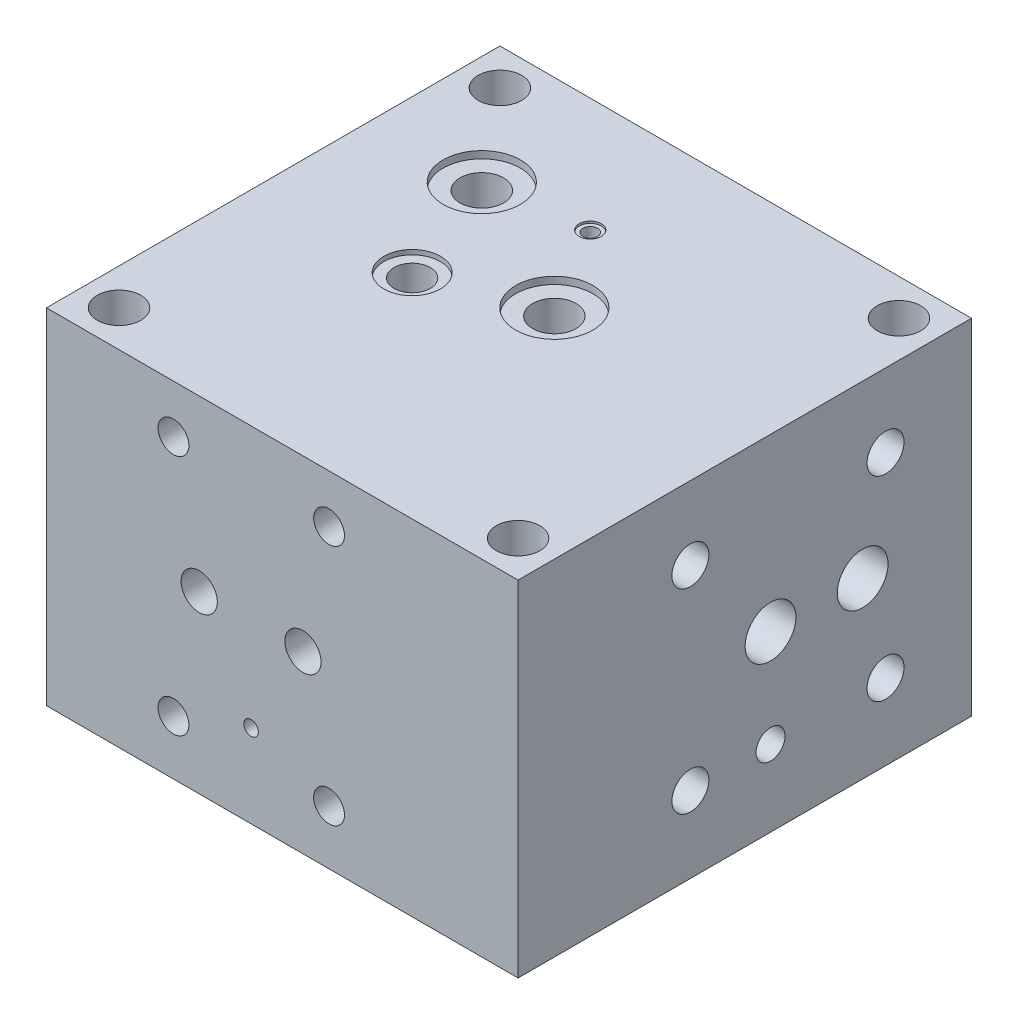
SolidWorks part; units mm, degrees
ref_plane "前视基准面" through (0, 0, 0) normal (0, 0, 1) x (1, 0, 0)
ref_plane "上视基准面" through (0, 0, 0) normal (0, 1, 0) x (1, 0, 0)
ref_plane "右视基准面" through (0, 0, 0) normal (1, 0, 0) x (0, 0, -1)
sketch "草图1" plane through (0, 0, 0) normal (0, 1, 0) x (1, 0, 0)
  line L1 (65, -62.5) -> (-65, -62.5)
  line L2 (65, -62.5) -> (65, 62.5)
  line L3 (65, 62.5) -> (-65, 62.5)
  line L4 (-65, -62.5) -> (-65, 62.5)
  line L5 (65, -62.5) -> (-65, 62.5) construction
  line L6 (65, 62.5) -> (-65, -62.5) construction
  point P0 (0, 0)
  dimension "D1" = 130
  dimension "D2" = 125
extrude "凸台-拉伸2" add sketch "草图1" along normal blind 95
sketch "草图2" plane through (0, 95, 0) normal (0, 1, 0) x (1, 0, 0)
  line L0 (-65, 62.5) -> (-65, -62.5) construction
  line L1 (65, 62.5) -> (-65, 62.5) construction
  line L2 (65, -62.5) -> (65, 62.5) construction
  line L3 (-65, -62.5) -> (65, -62.5) construction
  circle A0 centre (-55, 52.5) radius 6
  circle A1 centre (55, 52.5) radius 6
  circle A2 centre (-55, -52.5) radius 6
  dimension "D3" = 12
  dimension "D4" = 10
  dimension "D6" = 10
  dimension "D1" = 10
  dimension "D2" = 10
  dimension "D5" = 10
  dimension "D7" = 10
extrude "切除-拉伸1" cut sketch "草图2" against normal through all
sketch "草图3" plane through (0, 95, 0) normal (0, 1, 0) x (1, 0, 0)
  line L0 (65, -62.5) -> (65, 62.5) construction
  line L1 (-65, -62.5) -> (65, -62.5) construction
  circle A0 centre (55, -52.5) radius 6
  dimension "D1" = 10
  dimension "D2" = 10
extrude "切除-拉伸2" cut sketch "草图3" against normal blind 95
sketch "草图4" plane through (0, 95, 0) normal (0, 1, 0) x (1, 0, 0)
  line L0 (65, 62.5) -> (-65, 62.5) construction
  line L1 (-65, 62.5) -> (-65, -62.5) construction
  circle A0 centre (-35, 27.5) radius 10.65
  dimension "D1" = 21.3
  dimension "D2" = 35
  dimension "D3" = 30
extrude "切除-拉伸3" cut sketch "草图4" against normal blind 1.97
sketch "草图5" plane through (0, 93.03, 0) normal (0, 1, 0) x (1, 0, 0)
  circle A0 centre (-35, 27.5) radius 6
  dimension "D1" = 12
extrude "切除-拉伸5" cut sketch "草图5" against normal through all
sketch "草图6" plane through (0, 95, 0) normal (0, 1, 0) x (1, 0, 0)
  line L1 (-65, 62.5) -> (-65, -62.5) construction
  line L2 (-65, -62.5) -> (65, -62.5) construction
  circle A0 centre (5, 7.5) radius 10.65
  dimension "D1" = 21.3
  dimension "D2" = 70
  dimension "D3" = 70
extrude "切除-拉伸6" cut sketch "草图6" against normal blind 1.97
sketch "草图7" plane through (0, 93.03, 0) normal (0, 1, 0) x (1, 0, 0)
  circle A0 centre (5, 7.5) radius 6
extrude "切除-拉伸7" cut sketch "草图7" against normal through all
sketch "草图8" plane through (0, 95, 0) normal (0, 1, 0) x (1, 0, 0)
  line L0 (-65, -62.5) -> (65, -62.5) construction
  line L1 (-65, 62.5) -> (-65, -62.5) construction
  circle A0 centre (-23, -3.7) radius 7.8
  dimension "D1" = 15.6
  dimension "D2" = 58.8
  dimension "D3" = 42
extrude "切除-拉伸8" cut sketch "草图8" against normal blind 1.28
sketch "草图9" plane through (0, 93.72, 0) normal (0, 1, 0) x (1, 0, 0)
  circle A0 centre (-23, -3.7) radius 5
hole_wizard "大小mm 暗销孔1" positions "3D草图1" profile "草图10" hole size "Ø10.0" standard "GB"
sketch3d "3D草图1"
  point P0 (-23, 93.72, 3.7)
sketch "草图10" plane through (-23, 93.72, 3.7) normal (1, 0, 0) x (0, 0, 1)
  line L0 (0, 0) -> (0, 52.7343)
  line L1 (0, 52.7343) -> (5, 49.73)
  line L2 (5, 49.73) -> (5, 0)
  line L5 (5, 0) -> (0, 0)
  line L10 (0, 52.7343) -> (-5, 49.73) construction
  line L11 (0, -6.35) -> (0, 107.95) construction
  dimension "孔直径" = 10
  dimension "孔深度" = 49.73
  dimension "导头角度" = 118
hole_wizard "M10 螺纹孔2" positions "3D草图3" profile "草图12" tap size "M10" standard "GB"
sketch3d "3D草图3"
  line L0 (-65, 95, 62.5) -> (-65, 0, 62.5) construction
  line L1 (-65, 95, -62.5) -> (-65, 95, 62.5) construction
  point P0 (-65, 81.7, 39.4)
  dimension "D1" = 23.1
  dimension "D2" = 13.3
sketch "草图12" plane through (-65, 81.7, 39.4) normal (0, 1, 0) x (0, 0, 1)
  line L0 (0, 0) -> (0, 16.5537)
  line L1 (0, 16.5537) -> (4.25, 14)
  line L2 (4.25, 14) -> (4.25, 0)
  line L5 (4.25, 0) -> (0, 0)
  line L10 (0, 16.5537) -> (-4.25, 14) construction
  line L11 (0, -6.35) -> (0, 107.95) construction
  dimension "螺纹孔钻头直径" = 8.5
  dimension "螺纹孔钻头深度" = 14
  dimension "导头角度" = 118
cosmetic thread "孔螺蚊线2" parameters "D1"=10, "D2"=10
hole_wizard "M10 螺纹孔3" positions "3D草图4" profile "草图13" tap size "M10" standard "GB"
sketch3d "3D草图4"
  line L0 (-65, 95, -62.5) -> (-65, 95, 62.5) construction
  line L1 (-65, 95, -62.5) -> (-65, 0, -62.5) construction
  point P0 (-65, 81.7, -3.5)
  dimension "D1" = 13.3
  dimension "D2" = 59
sketch "草图13" plane through (-65, 81.7, -3.5) normal (0, 1, 0) x (0, 0, 1)
  line L0 (0, 0) -> (0, 16.5537)
  line L1 (0, 16.5537) -> (4.25, 14)
  line L2 (4.25, 14) -> (4.25, 0)
  line L5 (4.25, 0) -> (0, 0)
  line L10 (0, 16.5537) -> (-4.25, 14) construction
  line L11 (0, -6.35) -> (0, 107.95) construction
  dimension "螺纹孔钻头直径" = 8.5
  dimension "螺纹孔钻头深度" = 14
  dimension "导头角度" = 118
cosmetic thread "孔螺蚊线3" parameters "D1"=10, "D2"=10
hole_wizard "M10 螺纹孔4" positions "3D草图5" profile "草图14" tap size "M10" standard "GB"
sketch3d "3D草图5"
  line L0 (-65, 95, 62.5) -> (-65, 0, 62.5) construction
  line L1 (-65, 0, -62.5) -> (-65, 0, 62.5) construction
  point P0 (-65, 15, 39.4)
  dimension "D1" = 23.1
  dimension "D2" = 15
sketch "草图14" plane through (-65, 15, 39.4) normal (0, 1, 0) x (0, 0, 1)
  line L0 (0, 0) -> (0, 16.5537)
  line L1 (0, 16.5537) -> (4.25, 14)
  line L2 (4.25, 14) -> (4.25, 0)
  line L5 (4.25, 0) -> (0, 0)
  line L10 (0, 16.5537) -> (-4.25, 14) construction
  line L11 (0, -6.35) -> (0, 107.95) construction
  dimension "螺纹孔钻头直径" = 8.5
  dimension "螺纹孔钻头深度" = 14
  dimension "导头角度" = 118
cosmetic thread "孔螺蚊线4" parameters "D1"=10, "D2"=10
hole_wizard "M10 螺纹孔5" positions "3D草图6" profile "草图15" tap size "M10" standard "GB"
sketch3d "3D草图6"
  line L0 (-65, 0, -62.5) -> (-65, 0, 62.5) construction
  line L1 (-65, 95, -62.5) -> (-65, 0, -62.5) construction
  point P0 (-65, 15, -3.5)
  dimension "D1" = 15
  dimension "D2" = 59
sketch "草图15" plane through (-65, 15, -3.5) normal (0, 1, 0) x (0, 0, 1)
  line L0 (0, 0) -> (0, 16.5537)
  line L1 (0, 16.5537) -> (4.25, 14)
  line L2 (4.25, 14) -> (4.25, 0)
  line L5 (4.25, 0) -> (0, 0)
  line L10 (0, 16.5537) -> (-4.25, 14) construction
  line L11 (0, -6.35) -> (0, 107.95) construction
  dimension "螺纹孔钻头直径" = 8.5
  dimension "螺纹孔钻头深度" = 14
  dimension "导头角度" = 118
cosmetic thread "孔螺蚊线5" parameters "D1"=10, "D2"=10
hole_wizard "大小mm 暗销孔2" positions "3D草图7" profile "草图16" hole size "Ø8.0" standard "GB"
sketch3d "3D草图7"
  line L0 (-65, 95, -62.5) -> (-65, 95, 62.5) construction
  line L1 (-65, 95, -62.5) -> (-65, 0, -62.5) construction
  point P0 (-65, 81.7, 12.5)
  dimension "D1" = 13.3
  dimension "D2" = 75
sketch "草图16" plane through (-65, 81.7, 12.5) normal (0, 1, 0) x (0, 0, 1)
  line L0 (0, 0) -> (0, 12.4034)
  line L1 (0, 12.4034) -> (4, 10)
  line L2 (4, 10) -> (4, 0)
  line L5 (4, 0) -> (0, 0)
  line L10 (0, 12.4034) -> (-4, 10) construction
  line L11 (0, -6.35) -> (0, 107.95) construction
  dimension "孔直径" = 8
  dimension "孔深度" = 10
  dimension "导头角度" = 118
sketch "草图17" plane through (-65, 0, 0) normal (-1, 0, 0) x (0, 0, 1)
  line L0 (62.5, 95) -> (62.5, 0) construction
  line L1 (-62.5, 0) -> (62.5, 0) construction
  circle A0 centre (3.7, 48.3) radius 5
  dimension "D3" = 10
  dimension "D1" = 58.8
  dimension "D2" = 48.3
extrude "切除-拉伸9" cut sketch "草图17" against normal up to next
hole_wizard "大小mm 暗销孔4" positions "3D草图8" profile "草图20" hole size "Ø10.0" standard "GB"
sketch3d "3D草图8"
  line L0 (-65, 95, 62.5) -> (-65, 0, 62.5) construction
  line L1 (-65, 0, -62.5) -> (-65, 0, 62.5) construction
  point P0 (-65, 48.3, 32.3)
  dimension "D1" = 30.2
  dimension "D2" = 48.3
sketch "草图20" plane through (-65, 48.3, 32.3) normal (0, 1, 0) x (0, 0, 1)
  line L0 (0, 0) -> (0, 50.0043)
  line L1 (0, 50.0043) -> (5, 47)
  line L2 (5, 47) -> (5, 0)
  line L5 (5, 0) -> (0, 0)
  line L10 (0, 50.0043) -> (-5, 47) construction
  line L11 (0, -6.35) -> (0, 107.95) construction
  dimension "孔直径" = 10
  dimension "孔深度" = 47
  dimension "导头角度" = 118
hole_wizard "M10 螺纹孔7" positions "3D草图9" profile "草图23" tap size "M10" standard "GB"
sketch3d "3D草图9"
  line L0 (-65, 95, 62.5) -> (65, 95, 62.5) construction
  line L1 (65, 95, 62.5) -> (65, 0, 62.5) construction
  point P0 (12.9, 81.7, 62.5)
  dimension "D1" = 13.3
  dimension "D2" = 52.1
sketch "草图23" plane through (12.9, 81.7, 62.5) normal (1, 0, 0) x (0, -1, 0)
  line L0 (0, 0) -> (0, 16.5537)
  line L1 (0, 16.5537) -> (4.25, 14)
  line L2 (4.25, 14) -> (4.25, 0)
  line L5 (4.25, 0) -> (0, 0)
  line L10 (0, 16.5537) -> (-4.25, 14) construction
  line L11 (0, -6.35) -> (0, 107.95) construction
  dimension "螺纹孔钻头直径" = 8.5
  dimension "螺纹孔钻头深度" = 14
  dimension "导头角度" = 118
cosmetic thread "孔螺蚊线7" parameters "D1"=10, "D2"=10
hole_wizard "M10 螺纹孔8" positions "3D草图10" profile "草图24" tap size "M10" standard "GB"
sketch3d "3D草图10"
  line L0 (-65, 95, 62.5) -> (65, 95, 62.5) construction
  line L1 (-65, 95, 62.5) -> (-65, 0, 62.5) construction
  point P0 (-30, 81.7, 62.5)
  dimension "D1" = 13.3
  dimension "D2" = 35
sketch "草图24" plane through (-30, 81.7, 62.5) normal (1, 0, 0) x (0, -1, 0)
  line L0 (0, 0) -> (0, 16.5537)
  line L1 (0, 16.5537) -> (4.25, 14)
  line L2 (4.25, 14) -> (4.25, 0)
  line L5 (4.25, 0) -> (0, 0)
  line L10 (0, 16.5537) -> (-4.25, 14) construction
  line L11 (0, -6.35) -> (0, 107.95) construction
  dimension "螺纹孔钻头直径" = 8.5
  dimension "螺纹孔钻头深度" = 14
  dimension "导头角度" = 118
cosmetic thread "孔螺蚊线8" parameters "D1"=10, "D2"=10
hole_wizard "M10 螺纹孔9" positions "3D草图11" profile "草图25" tap size "M10" standard "GB"
sketch3d "3D草图11"
  line L0 (-65, 0, 62.5) -> (65, 0, 62.5) construction
  line L1 (65, 95, 62.5) -> (65, 0, 62.5) construction
  point P0 (12.9, 15, 62.5)
  dimension "D1" = 15
  dimension "D2" = 52.1
sketch "草图25" plane through (12.9, 15, 62.5) normal (1, 0, 0) x (0, -1, 0)
  line L0 (0, 0) -> (0, 16.5537)
  line L1 (0, 16.5537) -> (4.25, 14)
  line L2 (4.25, 14) -> (4.25, 0)
  line L5 (4.25, 0) -> (0, 0)
  line L10 (0, 16.5537) -> (-4.25, 14) construction
  line L11 (0, -6.35) -> (0, 107.95) construction
  dimension "螺纹孔钻头直径" = 8.5
  dimension "螺纹孔钻头深度" = 14
  dimension "导头角度" = 118
cosmetic thread "孔螺蚊线9" parameters "D1"=10, "D2"=10
hole_wizard "M10 螺纹孔10" positions "3D草图12" profile "草图26" tap size "M10" standard "GB"
sketch3d "3D草图12"
  line L0 (-65, 0, 62.5) -> (65, 0, 62.5) construction
  line L1 (-65, 95, 62.5) -> (-65, 0, 62.5) construction
  point P0 (-30, 15, 62.5)
  dimension "D1" = 15
  dimension "D2" = 35
sketch "草图26" plane through (-30, 15, 62.5) normal (1, 0, 0) x (0, -1, 0)
  line L0 (0, 0) -> (0, 16.5537)
  line L1 (0, 16.5537) -> (4.25, 14)
  line L2 (4.25, 14) -> (4.25, 0)
  line L5 (4.25, 0) -> (0, 0)
  line L10 (0, 16.5537) -> (-4.25, 14) construction
  line L11 (0, -6.35) -> (0, 107.95) construction
  dimension "螺纹孔钻头直径" = 8.5
  dimension "螺纹孔钻头深度" = 14
  dimension "导头角度" = 118
cosmetic thread "孔螺蚊线10" parameters "D1"=10, "D2"=10
sketch "草图27" plane through (0, 0, 62.5) normal (0, 0, 1) x (1, 0, 0)
  line L0 (-65, 95) -> (-65, 0) construction
  line L1 (-65, 0) -> (65, 0) construction
  circle A0 centre (-22.9, 48.3) radius 5
  dimension "D1" = 42.1
  dimension "D2" = 48.3
extrude "切除-拉伸10" cut sketch "草图27" against normal up to next
sketch "草图28" plane through (0, 0, 62.5) normal (0, 0, 1) x (1, 0, 0)
  line L0 (65, 95) -> (65, 0) construction
  line L1 (-65, 0) -> (65, 0) construction
  circle A0 centre (5.7, 48.3) radius 5
  dimension "D1" = 10
  dimension "D2" = 59.3
  dimension "D3" = 48.3
extrude "切除-拉伸11" cut sketch "草图28" against normal up to next
hole_wizard "M12 螺纹孔1" positions "3D草图13" profile "草图30" tap size "M12" standard "GB"
sketch3d "3D草图13"
  line L0 (65, 95, -62.5) -> (65, 0, -62.5) construction
  line L1 (65, 95, 62.5) -> (65, 95, -62.5) construction
  point P0 (65, 74.8, -38.8)
  dimension "D1" = 23.7
  dimension "D2" = 20.2
sketch "草图30" plane through (65, 74.8, -38.8) normal (0, 1, 0) x (0, 0, -1)
  line L0 (0, 0) -> (0, 21.0644)
  line L1 (0, 21.0644) -> (5.1, 18)
  line L2 (5.1, 18) -> (5.1, 0)
  line L5 (5.1, 0) -> (0, 0)
  line L10 (0, 21.0644) -> (-5.1, 18) construction
  line L11 (0, -6.35) -> (0, 107.95) construction
  dimension "螺纹孔钻头直径" = 10.2
  dimension "螺纹孔钻头深度" = 18
  dimension "导头角度" = 118
cosmetic thread "孔螺蚊线11" parameters "D1"=16, "D2"=12
hole_wizard "M12 螺纹孔2" positions "3D草图14" profile "草图31" tap size "M12" standard "GB"
sketch3d "3D草图14"
  line L0 (65, 95, 62.5) -> (65, 95, -62.5) construction
  line L1 (65, 95, 62.5) -> (65, 0, 62.5) construction
  point P0 (65, 74.8, 15)
  dimension "D1" = 20.2
  dimension "D2" = 47.5
sketch "草图31" plane through (65, 74.8, 15) normal (0, 1, 0) x (0, 0, -1)
  line L0 (0, 0) -> (0, 21.0644)
  line L1 (0, 21.0644) -> (5.1, 18)
  line L2 (5.1, 18) -> (5.1, 0)
  line L5 (5.1, 0) -> (0, 0)
  line L10 (0, 21.0644) -> (-5.1, 18) construction
  line L11 (0, -6.35) -> (0, 107.95) construction
  dimension "螺纹孔钻头直径" = 10.2
  dimension "螺纹孔钻头深度" = 18
  dimension "导头角度" = 118
cosmetic thread "孔螺蚊线12" parameters "D1"=16, "D2"=12
hole_wizard "M12 螺纹孔3" positions "3D草图15" profile "草图32" tap size "M12" standard "GB"
sketch3d "3D草图15"
  line L0 (65, 95, 62.5) -> (65, 0, 62.5) construction
  line L1 (65, 0, 62.5) -> (65, 0, -62.5) construction
  point P0 (65, 21, 15)
  dimension "D1" = 47.5
  dimension "D2" = 21
sketch "草图32" plane through (65, 21, 15) normal (0, 1, 0) x (0, 0, -1)
  line L0 (0, 0) -> (0, 21.0644)
  line L1 (0, 21.0644) -> (5.1, 18)
  line L2 (5.1, 18) -> (5.1, 0)
  line L5 (5.1, 0) -> (0, 0)
  line L10 (0, 21.0644) -> (-5.1, 18) construction
  line L11 (0, -6.35) -> (0, 107.95) construction
  dimension "螺纹孔钻头直径" = 10.2
  dimension "螺纹孔钻头深度" = 18
  dimension "导头角度" = 118
cosmetic thread "孔螺蚊线13" parameters "D1"=16, "D2"=12
hole_wizard "M12 螺纹孔4" positions "3D草图16" profile "草图33" tap size "M12" standard "GB"
sketch3d "3D草图16"
  line L0 (65, 95, -62.5) -> (65, 0, -62.5) construction
  line L1 (65, 0, 62.5) -> (65, 0, -62.5) construction
  point P0 (65, 21, -38.8)
  dimension "D1" = 23.7
  dimension "D2" = 21
sketch "草图33" plane through (65, 21, -38.8) normal (0, 1, 0) x (0, 0, -1)
  line L0 (0, 0) -> (0, 21.0644)
  line L1 (0, 21.0644) -> (5.1, 18)
  line L2 (5.1, 18) -> (5.1, 0)
  line L5 (5.1, 0) -> (0, 0)
  line L10 (0, 21.0644) -> (-5.1, 18) construction
  line L11 (0, -6.35) -> (0, 107.95) construction
  dimension "螺纹孔钻头直径" = 10.2
  dimension "螺纹孔钻头深度" = 18
  dimension "导头角度" = 118
cosmetic thread "孔螺蚊线14" parameters "D1"=16, "D2"=12
hole_wizard "大小mm 暗销孔5" positions "3D草图17" profile "草图35" hole size "Ø10.0" standard "GB"
sketch3d "3D草图17"
  line L0 (65, 95, -62.5) -> (65, 0, -62.5) construction
  line L1 (65, 0, 62.5) -> (65, 0, -62.5) construction
  point P0 (65, 47.9, -7.1)
  dimension "D1" = 55.4
  dimension "D2" = 47.9
sketch "草图35" plane through (65, 47.9, -7.1) normal (0, 1, 0) x (0, 0, -1)
  line L0 (0, 0) -> (0, 64.206)
  line L1 (0, 64.206) -> (7, 60)
  line L2 (7, 60) -> (7, 0)
  line L5 (7, 0) -> (0, 0)
  line L10 (0, 64.206) -> (-7, 60) construction
  line L11 (0, -6.35) -> (0, 107.95) construction
  dimension "孔直径" = 14
  dimension "孔深度" = 60
  dimension "导头角度" = 118
hole_wizard "大小mm 暗销孔6" positions "3D草图18" profile "草图36" hole size "Ø10.0" standard "GB"
sketch3d "3D草图18"
  line L0 (65, 95, -62.5) -> (65, 0, -62.5) construction
  line L1 (65, 0, 62.5) -> (65, 0, -62.5) construction
  point P0 (65, 47.9, -32.5)
  dimension "D1" = 30
  dimension "D2" = 47.9
sketch "草图36" plane through (65, 47.9, -32.5) normal (0, 1, 0) x (0, 0, -1)
  line L0 (0, 0) -> (0, 104.206)
  line L1 (0, 104.206) -> (7, 100)
  line L2 (7, 100) -> (7, 0)
  line L5 (7, 0) -> (0, 0)
  line L10 (0, 104.206) -> (-7, 100) construction
  line L11 (0, -6.35) -> (0, 107.95) construction
  dimension "孔直径" = 14
  dimension "孔深度" = 100
  dimension "导头角度" = 118
hole_wizard "大小mm 暗销孔9" positions "3D草图19" profile "草图43" hole size "Ø8.0" standard "GB"
sketch3d "3D草图19"
  line L0 (65, 95, -62.5) -> (65, 0, -62.5) construction
  line L1 (65, 0, 62.5) -> (65, 0, -62.5) construction
  point P0 (65, 21, -7.1)
  dimension "D1" = 55.4
  dimension "D2" = 21
sketch "草图43" plane through (65, 21, -7.1) normal (0, 1, 0) x (0, 0, -1)
  line L0 (0, 0) -> (0, 12.4034)
  line L1 (0, 12.4034) -> (4, 10)
  line L2 (4, 10) -> (4, 0)
  line L5 (4, 0) -> (0, 0)
  line L10 (0, 12.4034) -> (-4, 10) construction
  line L11 (0, -6.35) -> (0, 107.95) construction
  dimension "孔直径" = 8
  dimension "孔深度" = 10
  dimension "导头角度" = 118
sketch "草图44" plane through (0, 0, -62.5) normal (0, 0, -1) x (-1, 0, 0)
  line L0 (65, 95) -> (65, 0) construction
  line L1 (-65, 95) -> (65, 95) construction
  circle A0 centre (21, 68) radius 2
  dimension "D1" = 44
  dimension "D2" = 27
extrude "切除-拉伸12" cut sketch "草图44" against normal up to next
hole_wizard "M10 螺纹孔11" positions "3D草图20" profile "草图45" tap size "M10" standard "GB"
sketch3d "3D草图20"
  line L0 (-21, 68, 0.7) -> (-21, 68, -62.5) construction
  point P0 (-21, 68, -62.5)
sketch "草图45" plane through (-21, 68, -62.5) normal (1, 0, 0) x (0, 1, 0)
  line L0 (0, 0) -> (0, 16.5537)
  line L1 (0, 16.5537) -> (4.25, 14)
  line L2 (4.25, 14) -> (4.25, 0)
  line L5 (4.25, 0) -> (0, 0)
  line L10 (0, 16.5537) -> (-4.25, 14) construction
  line L11 (0, -6.35) -> (0, 107.95) construction
  dimension "螺纹孔钻头直径" = 8.5
  dimension "螺纹孔钻头深度" = 14
  dimension "导头角度" = 118
cosmetic thread "孔螺蚊线15" parameters "D1"=12, "D2"=10
sketch "草图46" plane through (0, 95, 0) normal (0, 1, 0) x (1, 0, 0)
  line L0 (65, -62.5) -> (65, 62.5) construction
  line L1 (65, 62.5) -> (-65, 62.5) construction
  circle A0 centre (-8.6, 31) radius 3.05
  dimension "D1" = 6.1
  dimension "D2" = 73.6
  dimension "D3" = 31.5
extrude "切除-拉伸13" cut sketch "草图46" against normal blind 0.56
sketch "草图47" plane through (0, 94.44, 0) normal (0, 1, 0) x (1, 0, 0)
  circle A0 centre (-8.6, 31) radius 2
hole_wizard "大小mm 暗销孔10" positions "3D草图21" profile "草图48" hole size "Ø4.0" standard "GB"
sketch3d "3D草图21"
  point P0 (-8.6, 94.44, -31)
sketch "草图48" plane through (-8.6, 94.44, -31) normal (1, 0, 0) x (0, 0, 1)
  line L0 (0, 0) -> (0, 72.2017)
  line L1 (0, 72.2017) -> (2, 71)
  line L2 (2, 71) -> (2, 0)
  line L5 (2, 0) -> (0, 0)
  line L10 (0, 72.2017) -> (-2, 71) construction
  line L11 (0, -6.35) -> (0, 107.95) construction
  dimension "孔直径" = 4
  dimension "孔深度" = 71
  dimension "导头角度" = 118
hole_wizard "大小mm 暗销孔11" positions "草图50" profile "草图49" hole size "Ø4.0" standard "GB"
sketch "草图50" plane through (0, 0, 62.5) normal (0, 0, 1) x (1, 0, 0)
  line L0 (65, 95) -> (65, 0) construction
  line L1 (-65, 0) -> (65, 0) construction
  point P0 (-8.6, 22.9)
  dimension "D1" = 73.6
  dimension "D2" = 22.9
sketch "草图49" plane through (-8.6, 22.9, 62.5) normal (1, 0, 0) x (0, -1, 0)
  line L0 (0, 0) -> (0, 96.2017)
  line L1 (0, 96.2017) -> (2, 95)
  line L2 (2, 95) -> (2, 0)
  line L5 (2, 0) -> (0, 0)
  line L10 (0, 96.2017) -> (-2, 95) construction
  line L11 (0, -6.35) -> (0, 107.95) construction
  dimension "孔直径" = 4
  dimension "孔深度" = 95
  dimension "导头角度" = 118
